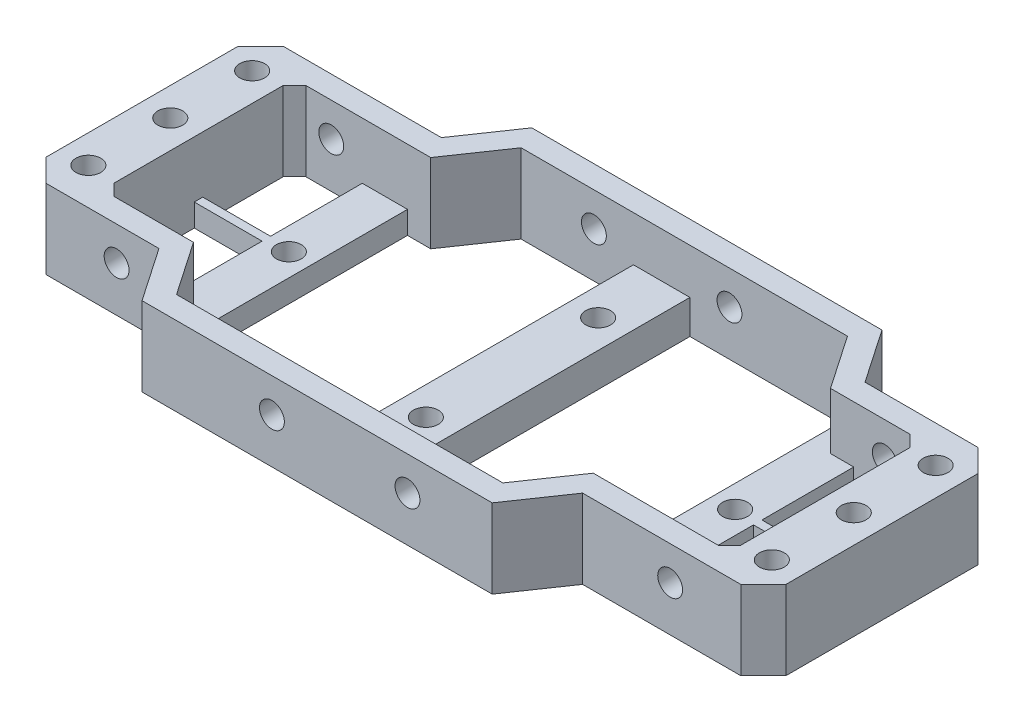
SolidWorks part; units mm, degrees
ref_plane "Front Plane" through (0, 0, 0) normal (0, 0, 1) x (1, 0, 0)
ref_plane "Top Plane" through (0, 0, 0) normal (0, 1, 0) x (1, 0, 0)
ref_plane "Right Plane" through (0, 0, 0) normal (1, 0, 0) x (0, 0, -1)
sketch "Sketch1" plane through (0, 0, 0) normal (0, 1, 0) x (1, 0, 0)
  line L0 (-104.176, 0) -> (26.824, 0) construction
  line L1 (-104.176, -21) -> (-104.176, 21)
  line L2 (26.824, 21) -> (26.824, -21)
  line L3 (-104.176, 21) -> (-72.176, 21)
  line L4 (-94.176, -17) -> (-94.176, 17)
  line L5 (-104.176, -21) -> (-80.176, -21)
  line L6 (26.824, 21) -> (2.824, 21)
  line L7 (26.824, -21) -> (-5.176, -21)
  line L8 (16.824, 17) -> (16.824, -17)
  line L9 (-73.676, -30.5) -> (-11.676, -30.5)
  line L10 (-65.676, 30.5) -> (-3.676, 30.5)
  line L11 (-72.176, 21) -> (-65.676, 30.5)
  line L12 (-3.676, 30.5) -> (2.824, 21)
  line L13 (-80.176, -21) -> (-73.676, -30.5)
  line L14 (-11.676, -30.5) -> (-5.176, -21)
  line L15 (-63.5662, 26.5) -> (-5.7858, 26.5)
  line L16 (-71.5662, -26.5) -> (-13.7858, -26.5)
  line L17 (-94.176, -17) -> (-78.0662, -17)
  line L18 (-71.5662, -26.5) -> (-78.0662, -17)
  line L19 (16.824, -17) -> (-7.2858, -17)
  line L20 (-13.7858, -26.5) -> (-7.2858, -17)
  line L21 (-94.176, 17) -> (-70.0662, 17)
  line L22 (-70.0662, 17) -> (-63.5662, 26.5)
  line L23 (16.824, 17) -> (0.7142, 17)
  line L24 (0.7142, 17) -> (-5.7858, 26.5)
  dimension "D1" = 131
  dimension "D2" = 42
  dimension "D3" = 32
  dimension "D4" = 34
  dimension "D5" = 4
  dimension "D6" = 24
  dimension "D7" = 24
  dimension "D8" = 32
  dimension "D9" = 10
  dimension "D10" = 4
  dimension "D11" = 10
  dimension "D12" = 62
  dimension "D13" = 62
  dimension "D14" = 6.5
  dimension "D15" = 61
  dimension "D16" = 9.5
  dimension "D17" = 6.5
  dimension "D18" = 4
  dimension "D19" = 4
  dimension "D20" = 4
  dimension "D21" = 4
  dimension "D22" = 4
  dimension "D23" = 4
  dimension "D24" = 4
extrude "Boss-Extrude1" add sketch "Sketch1" along normal blind 14
sketch "Sketch2" plane through (0, 0, 0) normal (0, -1, 0) x (-1, 0, 0)
  line L0 (104.176, -21) -> (80.176, -21) construction
  line L1 (72.176, 21) -> (104.176, 21) construction
  line L2 (-26.824, 21) -> (-2.824, 21) construction
  line L3 (5.176, -21) -> (-26.824, -21) construction
  line L4 (104.176, 21) -> (104.176, -21) construction
  line L5 (-26.824, -21) -> (-26.824, 21) construction
  circle A0 centre (99.176, 14.5) radius 2.2
  circle A1 centre (99.176, 0) radius 2.2
  circle A2 centre (99.176, -14.5) radius 2.2
  circle A3 centre (-21.824, -14.5) radius 2.2
  circle A4 centre (-21.824, 0) radius 2.2
  circle A5 centre (-21.824, 14.5) radius 2.2
  dimension "D1" = 4.4
  dimension "D2" = 4.4
  dimension "D3" = 4.4
  dimension "D4" = 4.4
  dimension "D5" = 4.4
  dimension "D6" = 4.4
  dimension "D10" = 6.5
  dimension "D16" = 5
  dimension "D17" = 5
  dimension "D18" = 5
  dimension "D7" = 6.5
  dimension "D8" = 21
  dimension "D9" = 6.5
  dimension "D11" = 21
  dimension "D12" = 6.5
  dimension "D13" = 5
  dimension "D14" = 5
  dimension "D15" = 5
extrude "Cut-Extrude1" cut sketch "Sketch2" against normal up to next
sketch "Sketch5" plane through (0, 0, -30.5) normal (0, 0, -1) x (-1, 0, 0)
  line L0 (104.176, 14) -> (104.176, 0) construction
  line L1 (72.176, 14) -> (104.176, 14) construction
  line L2 (3.676, 14) -> (65.676, 14) construction
  line L3 (-26.824, 14) -> (-2.824, 14) construction
  line L4 (-26.824, 14) -> (-26.824, 0) construction
  circle A0 centre (50.676, 8) radius 2.2
  circle A1 centre (26.676, 8) radius 2.2
  circle A2 centre (87.676, 8) radius 2.2
  circle A3 centre (-10.324, 8) radius 2.2
  dimension "D1" = 4.4
  dimension "D2" = 4.4
  dimension "D3" = 4.4
  dimension "D4" = 4.4
  dimension "D6" = 6
  dimension "D7" = 6
  dimension "D8" = 6
  dimension "D9" = 6
  dimension "D10" = 16.5
  dimension "D11" = 24
  dimension "D5" = 16.5
  dimension "D12" = 53.5
extrude "Cut-Extrude2" cut sketch "Sketch5" against normal through all
sketch "Sketch6" plane through (0, 0, 26.5) normal (0, 0, -1) x (-1, 0, 0)
  line L0 (71.5662, 0) -> (13.7858, 0) construction
  line L1 (43.676, 0) -> (33.676, 0)
  line L2 (43.676, 0) -> (43.676, 6)
  line L3 (43.676, 6) -> (33.676, 6)
  line L4 (33.676, 0) -> (33.676, 6)
  circle A0 centre (50.676, 8) radius 2.2 construction
  dimension "D1" = 10
  dimension "D2" = 7
  dimension "D3" = 6
extrude "Boss-Extrude2" add sketch "Sketch6" along normal up to next
sketch "Sketch7" plane through (0, 0, 0) normal (0, -1, 0) x (1, 0, 0)
  line L0 (-82.176, 17) -> (-82.176, -17)
  line L1 (-94.176, 17) -> (-78.0662, 17) construction
  line L2 (-70.0662, -17) -> (-94.176, -17) construction
  line L3 (-94.176, -17) -> (-94.176, 17) construction
  line L4 (-94.176, 0.75) -> (-82.176, 0.75)
  line L5 (-94.176, -0.75) -> (-82.176, -0.75)
  line L6 (-74.176, 22.6856) -> (-74.176, -17)
  line L7 (-78.0662, 17) -> (-71.5662, 26.5) construction
  line L8 (-82.176, 17) -> (-78.0662, 17)
  line L9 (-78.0662, 17) -> (-74.176, 22.6856)
  line L10 (-82.176, -17) -> (-74.176, -17)
  line L11 (4.824, 17) -> (4.824, -17)
  line L12 (-7.2858, 17) -> (16.824, 17) construction
  line L13 (16.824, -17) -> (0.7142, -17) construction
  line L14 (16.824, 17) -> (16.824, -17) construction
  line L15 (4.824, 0.75) -> (16.824, 0.75)
  line L16 (4.824, -0.75) -> (16.824, -0.75)
  line L17 (-3.176, 17) -> (-3.176, -22.6856)
  line L19 (0.7142, -17) -> (-5.7858, -26.5) construction
  circle A0 centre (-78.176, 0) radius 2.2
  circle A1 centre (0.824, 0) radius 2.2
  line M5 (-70.0662, -17) -> (-94.176, -17)
  line M6 (-94.176, -17) -> (-94.176, 17)
  line M7 (-94.176, 17) -> (-78.0662, 17)
  line M8 (-78.0662, 17) -> (-71.5662, 26.5)
  line M30 (-7.2858, 17) -> (16.824, 17)
  line M31 (16.824, 17) -> (16.824, -17)
  line M32 (16.824, -17) -> (0.7142, -17)
  line M33 (0.7142, -17) -> (-5.7858, -26.5)
  dimension "D5" = 4.4
  dimension "D9" = 4.4
  dimension "D11" = 4
  dimension "D1" = 12
  dimension "D2" = 16.25
  dimension "D3" = 16.25
  dimension "D4" = 8
  dimension "D6" = 12
  dimension "D7" = 16.25
  dimension "D8" = 8
  dimension "D10" = 4
extrude "Boss-Extrude3" add sketch "Sketch7" against normal blind 4 contours L5 L0 L4 M6 | L6 L0 A0 M8 M7 M5 | L17 L11 A1 M30 M33 M32 | L11 L16 L15 M31
sketch "Sketch8" plane through (0, 0, 0) normal (0, -1, 0) x (-1, 0, 0)
  line L0 (73.676, -30.5) -> (11.676, -30.5) construction
  line L1 (3.676, 30.5) -> (65.676, 30.5) construction
  line L2 (43.676, 26.5) -> (43.676, -26.5) construction
  circle A0 centre (38.676, -15.25) radius 2.2
  circle A1 centre (38.676, 15.25) radius 2.2
  dimension "D1" = 4.4
  dimension "D2" = 4.4
  dimension "D3" = 15.25
  dimension "D4" = 15.25
  dimension "D6" = 5
  dimension "D5" = 5
extrude "Cut-Extrude3" cut sketch "Sketch8" against normal up to next
chamfer "Chamfer1" distance 4 angle 45 4 edges at (-104.176, 7, 21) (26.824, 7, 21) (26.824, 7, -21) (-104.176, 7, -21)
chamfer "Chamfer2" distance 2 angle 45 4 edges at (16.824, 7, -17) (16.824, 7, 17) (-94.176, 7, -17) (-94.176, 7, 17)
